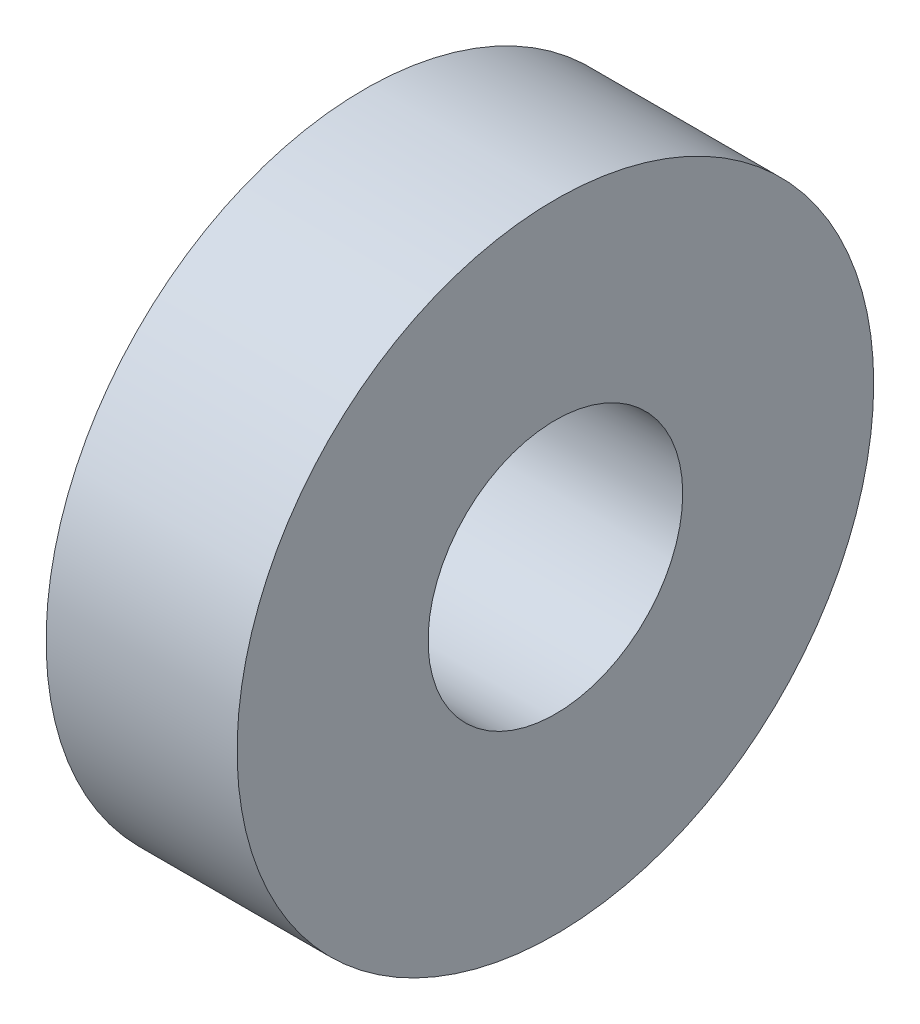
SolidWorks part; units mm, degrees
material "Pine"
ref_plane "Front Plane" through (0, 0, 0) normal (0, 0, 1) x (1, 0, 0)
ref_plane "Top Plane" through (0, 0, 0) normal (0, 1, 0) x (1, 0, 0)
ref_plane "Right Plane" through (0, 0, 0) normal (1, 0, 0) x (0, 0, -1)
sketch "Sketch1" plane through (0, 0, 0) normal (1, 0, 0) x (0, 0, -1)
  circle A0 centre (0, 0) radius 5
extrude "Boss-Extrude1" add sketch "Sketch1" along normal blind 3
sketch "Sketch2" plane through (3, 0, 0) normal (1, 0, 0) x (0, 0, -1)
  circle A0 centre (0, 0) radius 2
  dimension "D1" = 4
extrude "Cut-Extrude1" cut sketch "Sketch2" against normal through all
